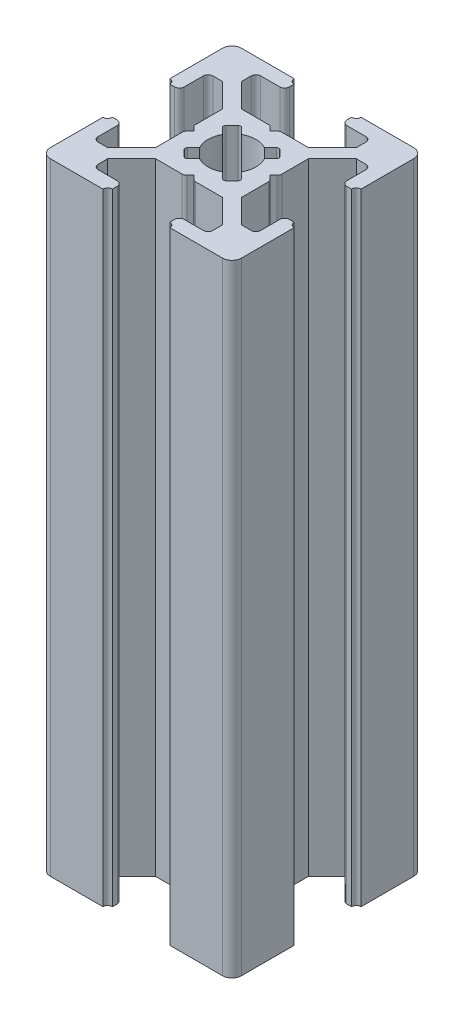
SolidWorks part; units mm, degrees
ref_plane "Front Plane" through (0, 0, 0) normal (0, 0, 1) x (1, 0, 0)
ref_plane "Top Plane" through (0, 0, 0) normal (0, 1, 0) x (1, 0, 0)
ref_plane "Right Plane" through (0, 0, 0) normal (1, 0, 0) x (0, 0, -1)
sketch "Sketch3" plane through (0, 0, 0) normal (0, 1, 0) x (1, 0, 0)
  line L0 (7, 20) -> (7, 18.5)
  line L1 (0, 0) -> (20, 0)
  line L2 (0, 0) -> (0, 20)
  line L3 (0, 20) -> (20, 20)
  line L4 (20, 0) -> (20, 20)
  line L5 (7, 18.5) -> (4, 18.5)
  line L6 (4, 18.5) -> (4, 17)
  line L7 (4, 17) -> (6.5, 14.5)
  line L8 (6.5, 14.5) -> (13.5, 14.5)
  line L9 (13.5, 14.5) -> (16, 17)
  line L10 (16, 17) -> (16, 18.5)
  line L11 (16, 18.5) -> (13, 18.5)
  line L12 (13, 18.5) -> (13, 20)
  line L13 (13, 20) -> (7, 20)
  line L14 (9.5, 14.5) -> (10, 14)
  line L15 (10, 14) -> (10.5, 14.5)
  line L16 (10.5, 14.5) -> (9.5, 14.5)
  line L17 (13, 19.5) -> (13, 20)
  line L18 (13.5, 20) -> (13, 20)
  line L19 (7, 19.5) -> (7, 20)
  line L20 (6.5, 20) -> (7, 20)
  line L21 (0, 13) -> (1.5, 13)
  line L22 (1.5, 13) -> (1.5, 16)
  line L23 (1.5, 16) -> (3, 16)
  line L24 (3, 16) -> (5.5, 13.5)
  line L25 (5.5, 13.5) -> (5.5, 6.5)
  line L26 (5.5, 6.5) -> (3, 4)
  line L27 (3, 4) -> (1.5, 4)
  line L28 (1.5, 4) -> (1.5, 7)
  line L29 (1.5, 7) -> (0, 7)
  line L30 (0, 7) -> (0, 13)
  line L31 (5.5, 10.5) -> (5.5, 9.5)
  line L32 (5.5, 9.5) -> (6, 10)
  line L33 (6, 10) -> (5.5, 10.5)
  line L34 (0.5, 13) -> (0, 13)
  line L35 (0, 13.5) -> (0, 13)
  line L36 (0, 6.5) -> (0, 7)
  line L37 (0.5, 7) -> (0, 7)
  line L38 (10, 20) -> (10, 0) construction
  line L39 (20, 10) -> (0, 10) construction
  line L40 (10, 6) -> (10.5, 5.5)
  line L41 (9.5, 5.5) -> (10, 6)
  line L42 (10.5, 5.5) -> (9.5, 5.5)
  line L43 (13.5, 0) -> (13, 0)
  line L44 (13, 0.5) -> (13, 0)
  line L45 (6.5, 0) -> (7, 0)
  line L46 (7, 0.5) -> (7, 0)
  line L47 (13, 1.5) -> (13, 0)
  line L48 (16, 1.5) -> (13, 1.5)
  line L49 (16, 3) -> (16, 1.5)
  line L50 (13.5, 5.5) -> (16, 3)
  line L51 (6.5, 5.5) -> (13.5, 5.5)
  line L52 (4, 3) -> (6.5, 5.5)
  line L53 (4, 1.5) -> (4, 3)
  line L54 (7, 1.5) -> (4, 1.5)
  line L55 (7, 0) -> (7, 1.5)
  line L56 (13, 0) -> (7, 0)
  line L57 (14.5, 9.5) -> (14, 10)
  line L58 (14.5, 10.5) -> (14.5, 9.5)
  line L59 (14, 10) -> (14.5, 10.5)
  line L60 (19.5, 7) -> (20, 7)
  line L61 (20, 6.5) -> (20, 7)
  line L62 (20, 13.5) -> (20, 13)
  line L63 (19.5, 13) -> (20, 13)
  line L64 (18.5, 7) -> (20, 7)
  line L65 (18.5, 4) -> (18.5, 7)
  line L66 (17, 4) -> (18.5, 4)
  line L67 (14.5, 6.5) -> (17, 4)
  line L68 (14.5, 13.5) -> (14.5, 6.5)
  line L69 (17, 16) -> (14.5, 13.5)
  line L70 (18.5, 16) -> (17, 16)
  line L71 (18.5, 13) -> (18.5, 16)
  line L72 (20, 13) -> (18.5, 13)
  line L73 (20, 7) -> (20, 13)
  arc A0 (13.5, 20) -> (13, 19.5) centre (13, 20) cw
  arc A1 (6.5, 20) -> (7, 19.5) centre (7, 20) ccw
  arc A2 (0.5, 13) -> (0, 13.5) centre (0, 13) ccw
  arc A3 (0.5, 7) -> (0, 6.5) centre (0, 7) cw
  arc A4 (13.5, 0) -> (13, 0.5) centre (13, 0) ccw
  arc A5 (6.5, 0) -> (7, 0.5) centre (7, 0) cw
  arc A6 (19.5, 7) -> (20, 6.5) centre (20, 7) ccw
  arc A7 (19.5, 13) -> (20, 13.5) centre (20, 13) cw
  point P7 (10, 14.5)
  point P16 (10, 20)
  point P26 (5.5, 10)
  point P35 (0, 10)
  dimension "D16" = 0.5
  dimension "D17" = 0.5
  dimension "D28" = 0.5
  dimension "D29" = 0.5
  dimension "D1" = 20
  dimension "D2" = 20
  dimension "D3" = 7
  dimension "D4" = 7
  dimension "D5" = 1.5
  dimension "D6" = 1.5
  dimension "D7" = 3
  dimension "D8" = 3
  dimension "D9" = 1.5
  dimension "D10" = 1.5
  dimension "D11" = 7
  dimension "D12" = 5.5
  dimension "D13" = 0.5
  dimension "D14" = 0.5
  dimension "D15" = 0.5
  dimension "D18" = 7
  dimension "D19" = 7
  dimension "D20" = 1.5
  dimension "D21" = 1.5
  dimension "D22" = 3
  dimension "D23" = 7
  dimension "D24" = 5.5
  dimension "D25" = 0.5
  dimension "D26" = 0.5
  dimension "D27" = 0.5
extrude "Boss-Extrude1" add sketch "Sketch3" along normal blind 65 contours L72 A7 L4 L3 A0 L12 L11 L10 L9 L8 L15 L14 L7 L6 L5 L0 A1 L2 A2 L21 L22 L23 L24 L25 L33 L32 L26 L27 L28 L29 A3 L1 A5 L55 L54 L53 L52 L51 L41 L40 L50 L49 L48 L47 A4
fillet "Fillet1" radius 1 4 edges at (0, 32.5, 0) (20, 32.5, 0) (20, 32.5, -20) (0, 32.5, -20)
sketch "Sketch4" plane through (0, 65, 0) normal (0, 1, 0) x (1, 0, 0)
  line L0 (13.5, 14.5) -> (5.5, 6.5) construction
  line L1 (14.5, 13.5) -> (6.5, 5.5) construction
  line L2 (10.5, 14.5) -> (14.5, 10.5) construction
  line L3 (12, 13) -> (13, 12)
  line L4 (13, 12) -> (8, 7)
  line L5 (8, 7) -> (7, 8)
  line L6 (7, 8) -> (12, 13)
  line L7 (13.5, 14.5) -> (16, 17) construction
  line L8 (17, 16) -> (14.5, 13.5) construction
  line L9 (5.5, 9.5) -> (9.5, 5.5) construction
  line L10 (5.5, 10.5) -> (9.5, 14.5) construction
  line L11 (14.5, 9.5) -> (10.5, 5.5) construction
  line L12 (6.5, 14.5) -> (14.5, 6.5) construction
  line L13 (5.5, 13.5) -> (13.5, 5.5) construction
  line L14 (7, 12) -> (8, 13)
  line L15 (8, 13) -> (13, 8)
  line L16 (13, 8) -> (12, 7)
  line L17 (12, 7) -> (7, 12)
  line L18 (4, 17) -> (6.5, 14.5) construction
  line L19 (3, 16) -> (5.5, 13.5) construction
  line L20 (20, 10) -> (0, 10) construction
  circle A0 centre (10, 10) radius 2.5
  dimension "D1" = 5
extrude "Cut-Extrude1" cut sketch "Sketch4" against normal through all contours L6 A0 L15 | L4 A0 L6 L15 | L15 A0 L17 L6 | L17 L4 L15 L6 | L17 A0 L6 | L6 A0 L4 L17 | L4 A0 L17 | L17 A0 L15 L4 | L15 A0 L4 | A0 L6 L5 L4 | A0 L17 L16 L15 | A0 L4 L3 L6 | A0 L15 L14 L17
fillet "Fillet2" radius 0.5 24 edges at (1.5, 32.5, -16) (1.5, 32.5, -13) (5.5, 32.5, -10.5) (5.5, 32.5, -9.5) (1.5, 32.5, -7) (1.5, 32.5, -4) (4, 32.5, -1.5) (7, 32.5, -1.5) (9.5, 32.5, -5.5) (10.5, 32.5, -5.5) (13, 32.5, -1.5) (16, 32.5, -1.5) (18.5, 32.5, -4) (18.5, 32.5, -7) (18.5, 32.5, -13) (18.5, 32.5, -16) (14.5, 32.5, -9.5) (14.5, 32.5, -10.5) (10.5, 32.5, -14.5) (9.5, 32.5, -14.5) (16, 32.5, -18.5) (13, 32.5, -18.5) (7, 32.5, -18.5) (4, 32.5, -18.5)
fillet "Fillet3" radius 0.25 8 edges at (13, 32.5, -8) (12, 32.5, -7) (13, 32.5, -12) (12, 32.5, -13) (8, 32.5, -13) (7, 32.5, -12) (7, 32.5, -8) (8, 32.5, -7)
